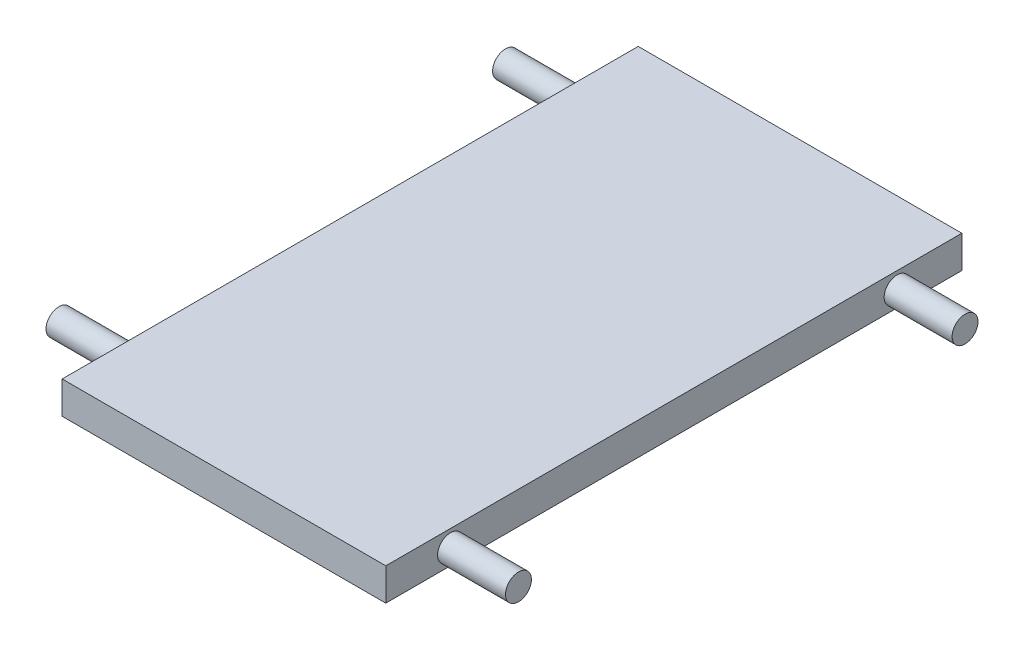
SolidWorks part; units mm, degrees
ref_plane "Front Plane" through (0, 0, 0) normal (0, 0, 1) x (1, 0, 0)
ref_plane "Top Plane" through (0, 0, 0) normal (0, 1, 0) x (1, 0, 0)
ref_plane "Right Plane" through (0, 0, 0) normal (1, 0, 0) x (0, 0, -1)
sketch "Sketch1" plane through (0, 0, 0) normal (0, 1, 0) x (1, 0, 0)
  line L1 (-250, -445) -> (250, -445)
  line L2 (-250, -445) -> (-250, 445)
  line L3 (-250, 445) -> (250, 445)
  line L4 (250, -445) -> (250, 445)
  line L5 (-250, -445) -> (250, 445) construction
  line L6 (-250, 445) -> (250, -445) construction
  point P0 (0, 0)
  dimension "D1" = 890
  dimension "D2" = 500
extrude "Boss-Extrude1" add sketch "Sketch1" along normal blind 50
sketch "Sketch2" plane through (250, 0, 0) normal (1, 0, 0) x (0, 0, -1)
  line L0 (445, 50) -> (445, 0) construction
  circle A0 centre (345, 24.2743) radius 20
  dimension "D1" = 40
  dimension "D2" = 100
extrude "Boss-Extrude2" add sketch "Sketch2" along normal blind 105
mirror "Mirror1" about plane through (0, 0, 0) normal (0, 0, 1) of "Boss-Extrude2"
mirror "Mirror2" about plane through (0, 0, 0) normal (1, 0, 0) of "Mirror1", "Boss-Extrude2"
